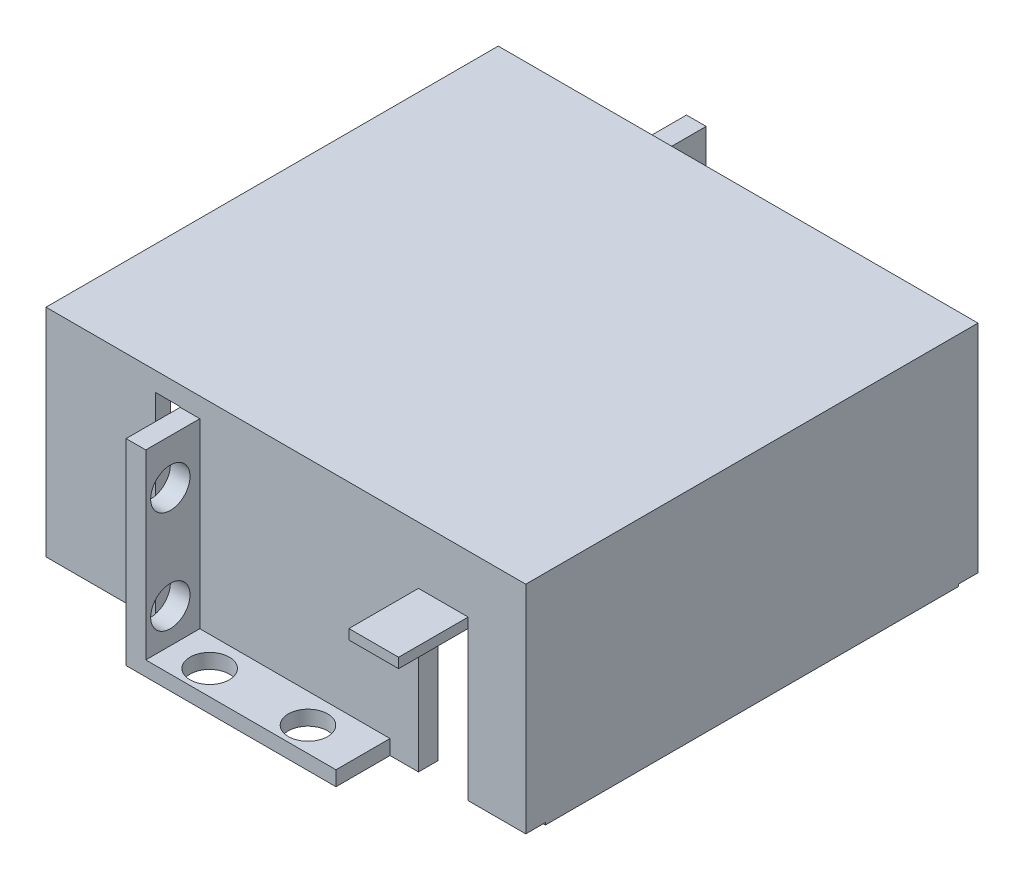
SolidWorks part; units mm, degrees
ref_plane "Front Plane" through (0, 0, 0) normal (0, 0, 1) x (1, 0, 0)
ref_plane "Top Plane" through (0, 0, 0) normal (0, 1, 0) x (1, 0, 0)
ref_plane "Right Plane" through (0, 0, 0) normal (1, 0, 0) x (0, 0, -1)
sketch "Sketch2" plane through (0, 0, 0) normal (1, 0, 0) x (0, 0, -1)
  line L0 (-7.5, 0) -> (-7.5, -4.5801) construction
  line L1 (0, 0) -> (-7.5, 0)
  line L2 (0, 0) -> (0, -20)
  line L3 (0, -20) -> (-7.5, -20)
  line L4 (-7.5, 0) -> (-7.5, -20)
  line L6 (-7.5, -20) -> (-7.5, -15) construction
  circle A0 centre (-5, -4.5801) radius 2
  circle A1 centre (-5, -15) radius 2
extrude "Boss-Extrude1" add sketch "Sketch2" along normal blind 2
sketch "Sketch4" plane through (0, 0, 0) normal (0, 0, 1) x (1, 0, 0)
  line L0 (0, -20) -> (22, -20) construction
  line L1 (0, 0) -> (21, 0)
  line L2 (0, 0) -> (0, -20)
  line L3 (0, -20) -> (21, -20)
  line L4 (21, 0) -> (21, -20)
extrude "Boss-Extrude2" add sketch "Sketch4" along normal blind 2
sketch "Sketch5" plane through (0, 0, 0) normal (0, 1, 0) x (1, 0, 0)
  line L1 (21, -2) -> (0, -2)
  line L2 (21, -2) -> (21, 44)
  line L3 (21, 44) -> (0, 44)
  line L4 (0, -2) -> (0, 44)
extrude "Boss-Extrude3" add sketch "Sketch5" along normal blind 2
sketch "Sketch6" plane through (0, 2, 0) normal (0, 1, 0) x (1, 0, 0)
  line L0 (21, -2) -> (21, 44) construction
  line L1 (0, 44) -> (21, 44)
  line L2 (0, 44) -> (0, 42)
  line L3 (0, 42) -> (21, 42)
  line L4 (21, 44) -> (21, 42)
extrude "Boss-Extrude4" add sketch "Sketch6" against normal blind 22
sketch "Sketch7" plane through (0, 0, 0) normal (-1, 0, 0) x (0, 0, 1)
  line L0 (-49.5, 0) -> (-49.5, -5)
  line L1 (-43, 0) -> (-49.5, 0)
  line L2 (-43, 0) -> (-43, -20)
  line L3 (-43, -20) -> (-49.5, -20)
  line L4 (-49.5, 0) -> (-49.5, -20)
  line L6 (-49.5, -20) -> (-49.5, -15)
  circle A0 centre (-47, -5) radius 2
  circle A1 centre (-47, -15) radius 2
extrude "Boss-Extrude7" add sketch "Sketch7" against normal blind 2 contours L0 L4 L3 L1 A1 A0
sketch "Sketch8" plane through (0, -20, 0) normal (0, -1, 0) x (1, 0, 0)
  line L0 (1, -49.5) -> (6, -49.5)
  line L5 (1, -43) -> (21, -43)
  line L6 (1, -43) -> (1, -49.5)
  line L7 (1, -49.5) -> (21, -49.5)
  line L8 (21, -43) -> (21, -49.5)
  line L10 (21, -49.5) -> (16, -49.5)
  circle A0 centre (6, -47) radius 2
  circle A1 centre (16, -47) radius 2
extrude "Boss-Extrude9" add sketch "Sketch8" against normal blind 1.5 contours A1 | L6 L5 L8 L7 | A0
sketch "Sketch9" plane through (0, -20, 0) normal (0, -1, 0) x (1, 0, 0)
  line L0 (21, 7.5) -> (16, 7.5)
  line L1 (1, 1) -> (21, 1)
  line L2 (1, 1) -> (1, 7.5)
  line L3 (1, 7.5) -> (21, 7.5)
  line L4 (21, 1) -> (21, 7.5)
  line L6 (16, 7.5) -> (6, 7.5)
  circle A0 centre (6, 5) radius 2
  circle A1 centre (16, 5) radius 2
  line M10 (21, 2) -> (2, 2)
  line M11 (2, 2) -> (2, 7.5)
extrude "Boss-Extrude10" add sketch "Sketch9" against normal blind 1.5 contours L4 L0 L3 A1 A0 M10 M11
scale "Scale1" scale about centroid uniform scaling yes scale factor 0.98
scale "Scale2" scale about centroid uniform scaling yes scale factor 0.98
scale "Scale3" scale about centroid uniform scaling yes scale factor 1.03
sketch "Sketch10" plane through (0, 1.9196, 0) normal (0, 1, 0) x (1, 0, 0)
  line L0 (0.1057, -1.7519) -> (20.8791, -1.7519)
sketch "Sketch11" plane through (20.8791, 0, 0) normal (1, 0, 0) x (0, 0, -1)
  line L0 (-1.7519, 1.9196) -> (43.7519, 1.9196)
  line L1 (43.7519, 1.9196) -> (43.7519, -18.3593)
  line L2 (43.7519, -18.3593) -> (49.1925, -18.3593)
  line L3 (49.1925, -18.3593) -> (49.1925, -19.8431)
  line L4 (49.1925, -19.8431) -> (41.7735, -19.8431)
  line L5 (41.7735, -19.8431) -> (41.7735, -0.0589)
  line L6 (41.7735, -0.0589) -> (0.2265, -0.0589)
  line L7 (0.2265, -0.0589) -> (0.2265, -19.8431)
  line L8 (0.2265, -19.8431) -> (-7.1925, -19.8431)
  line L9 (-7.1925, -19.8431) -> (-7.1925, -18.3593)
  line L10 (-7.1925, -18.3593) -> (-1.7519, -18.3593)
  line L11 (-1.7519, -18.3593) -> (-1.7519, 1.9196)
extrude "Boss-Extrude11" add sketch "Sketch11" along normal blind 14
sketch "Sketch13" plane through (0, -0.0589, 0) normal (0, -1, 0) x (-1, 0, 0)
  line L0 (-34.8791, 0.2265) -> (-0.1057, 0.2265) construction
  line L1 (-34.8791, 41.7735) -> (-33.8791, 41.7735)
  line L2 (-34.8791, 41.7735) -> (-34.8791, 0.2265)
  line L3 (-34.8791, 0.2265) -> (-33.8791, 0.2265)
  line L4 (-33.8791, 41.7735) -> (-33.8791, 0.2265)
  line L5 (-0.1057, 41.7735) -> (-34.8791, 41.7735) construction
extrude "Boss-Extrude12" add sketch "Sketch13" along normal blind 20
sketch "Sketch15" plane through (0, -18.3593, 0) normal (0, 1, 0) x (1, 0, 0)
  line L0 (34.8791, 43.7519) -> (2.0841, 43.7519) construction
  line L1 (34.8791, 49.1925) -> (21.2229, 49.1925)
  line L2 (34.8791, 49.1925) -> (34.8791, 43.7519)
  line L3 (34.8791, 43.7519) -> (21.2229, 43.7519)
  line L4 (21.2229, 49.1925) -> (21.2229, 43.7519)
extrude "Cut-Extrude1" cut sketch "Sketch15" against normal blind 20
sketch "Sketch16" plane through (0, -18.3593, 0) normal (0, 1, 0) x (1, 0, 0)
  line L0 (34.8791, -1.7519) -> (2.0841, -1.7519) construction
  line L1 (34.8791, -7.1925) -> (21.2229, -7.1925)
  line L2 (34.8791, -7.1925) -> (34.8791, -1.7519)
  line L3 (34.8791, -1.7519) -> (21.2229, -1.7519)
  line L4 (21.2229, -7.1925) -> (21.2229, -1.7519)
extrude "Cut-Extrude2" cut sketch "Sketch16" against normal blind 20
sketch "Sketch17" plane through (0.1057, 0, 0) normal (-1, 0, 0) x (0, 0, 1)
  line L0 (-43.7519, 1.9196) -> (1.7519, 1.9196)
  line L1 (1.7519, 1.9196) -> (1.7519, -0.0589) construction
  line L2 (-43.7519, 1.9196) -> (1.7519, 1.9196) construction
  line L3 (7.1925, -19.8431) -> (-0.2265, -19.8431) construction
  line L4 (1.7519, -19.8431) -> (-0.2265, -19.8431)
  line L5 (1.7519, 1.9196) -> (1.7519, -19.8431)
  line L6 (-0.2265, -19.8431) -> (1.7519, -19.8431)
  line L7 (-0.2265, -19.8431) -> (-0.2265, -0.0589)
  line L8 (-0.2265, -0.0589) -> (-41.7735, -0.0589)
  line L9 (-41.7735, -0.0589) -> (-41.7735, -19.8431)
  line L10 (-41.7735, -19.8431) -> (-43.7519, -19.8431)
  line L11 (-49.1925, -19.8431) -> (-41.7735, -19.8431) construction
  line L12 (-43.7519, -19.8431) -> (-43.7519, 1.9196)
  line M1 (1.7519, -0.0589) -> (1.7519, 1.9196)
  line M2 (1.7519, 1.9196) -> (-43.7519, 1.9196)
  line M3 (-43.7519, 1.9196) -> (-43.7519, -0.0589)
  line M6 (-49.1925, -19.8431) -> (-41.7735, -19.8431)
  line M7 (-41.7735, -19.8431) -> (-41.7735, -0.0589)
  line M8 (-41.7735, -0.0589) -> (-0.2265, -0.0589)
  line M9 (-0.2265, -0.0589) -> (-0.2265, -19.8431)
  line M10 (-0.2265, -19.8431) -> (7.1925, -19.8431)
extrude "Boss-Extrude13" add sketch "Sketch17" along normal blind 13.5 contours L12 L5 M6 M7 M8 M9 M10 M1 M2 M3
sketch "Sketch18" plane through (0, 0, 1.7519) normal (0, 0, 1) x (1, 0, 0)
  line L1 (0.1057, -19.8431) -> (-2.3943, -19.8431)
  line L2 (0.1057, -19.8431) -> (0.1057, 0)
  line L3 (0.1057, 0) -> (-2.3943, 0)
  line L4 (-2.3943, -19.8431) -> (-2.3943, 0)
  dimension "D1" = 2.5
extrude "Cut-Extrude3" cut sketch "Sketch18" against normal through all
sketch "Sketch19" plane through (0, -0.0589, 0) normal (0, -1, 0) x (1, 0, 0)
  line L0 (-2.3943, -0.2265) -> (-13.3943, -0.2265) construction
  line L1 (-13.3943, -41.7735) -> (-12.3943, -41.7735)
  line L2 (-13.3943, -41.7735) -> (-13.3943, -0.2265)
  line L3 (-13.3943, -0.2265) -> (-12.3943, -0.2265)
  line L4 (-12.3943, -41.7735) -> (-12.3943, -0.2265)
  dimension "D1" = 1
extrude "Boss-Extrude14" add sketch "Sketch19" along normal up to surface (19.7842 mm away) up to face at (15.9331, -19.8431, -48.6979)
sketch "Sketch20" plane through (0, 0, 1.7519) normal (0, 0, 1) x (1, 0, 0)
  line L0 (2.0841, -18.3593) -> (24.0841, -18.3593)
  line L1 (34.8791, -19.8431) -> (21.2229, -19.8431) construction
  line L2 (24.0841, -19.8431) -> (29.0841, -19.8431)
  line L3 (24.0841, -19.8431) -> (24.0841, -4.8431)
  line L4 (24.0841, -4.8431) -> (29.0841, -4.8431)
  line L5 (29.0841, -19.8431) -> (29.0841, -4.8431)
  dimension "D1" = 22
  dimension "D2" = 5
  dimension "D3" = 15
extrude "Cut-Extrude4" cut sketch "Sketch20" against normal up to surface (1.9784 mm away) contours L3 L2 L5 L4
sketch "Sketch21" plane through (-13.3943, 0, 0) normal (-1, 0, 0) x (0, 0, 1)
  line L0 (1.7519, -19.8431) -> (-4.2481, -19.8431)
  line L1 (-43.7519, -19.8431) -> (1.7519, -19.8431) construction
  line L3 (-4.2481, -19.8431) -> (-14.2481, -19.8431)
  line L4 (-4.2481, -19.8431) -> (-4.2481, -5.8431)
  line L5 (-4.2481, -5.8431) -> (-14.2481, -5.8431)
  line L6 (-14.2481, -19.8431) -> (-14.2481, -5.8431)
  line M4 (-43.7519, -19.8431) -> (1.7519, -19.8431)
  dimension "D1" = 6
  dimension "D2" = 10
  dimension "D3" = 14
extrude "Cut-Extrude5" cut sketch "Sketch21" against normal blind 19.5 contours L6 L4 L5 M4
sketch "Sketch22" plane through (0, 0, 1.7519) normal (0, 0, 1) x (1, 0, 0)
  line L1 (24.0841, -4.8431) -> (29.0841, -4.8431)
  line L2 (24.0841, -4.8431) -> (24.0841, -3.8431)
  line L3 (24.0841, -3.8431) -> (29.0841, -3.8431)
  line L4 (29.0841, -4.8431) -> (29.0841, -3.8431)
  spline S0 degree 1 poles (24.0841, -4.8431) (29.0841, -4.8431) knots 0 0 1 1
  line M4 (24.0841, -4.8431) -> (29.0841, -4.8431)
  dimension "D1" = 1
extrude "Boss-Extrude15" add sketch "Sketch22" along normal blind 7 and the other way blind 2 contours L4 L3 L2 M4
sketch "Sketch23" plane through (0, 0, -43.7519) normal (0, 0, -1) x (-1, 0, 0)
  line L0 (2.3943, 0) -> (3.5943, 0)
  line L1 (3.5943, 0) -> (3.5943, -19.8431)
  line L2 (13.3943, -19.8431) -> (2.3943, -19.8431) construction
  line L3 (2.3943, 0) -> (2.3943, -19.8431)
  line L4 (2.3943, -19.8431) -> (3.5943, -19.8431)
extrude "Cut-Extrude9" cut sketch "Sketch23" against normal blind 44
